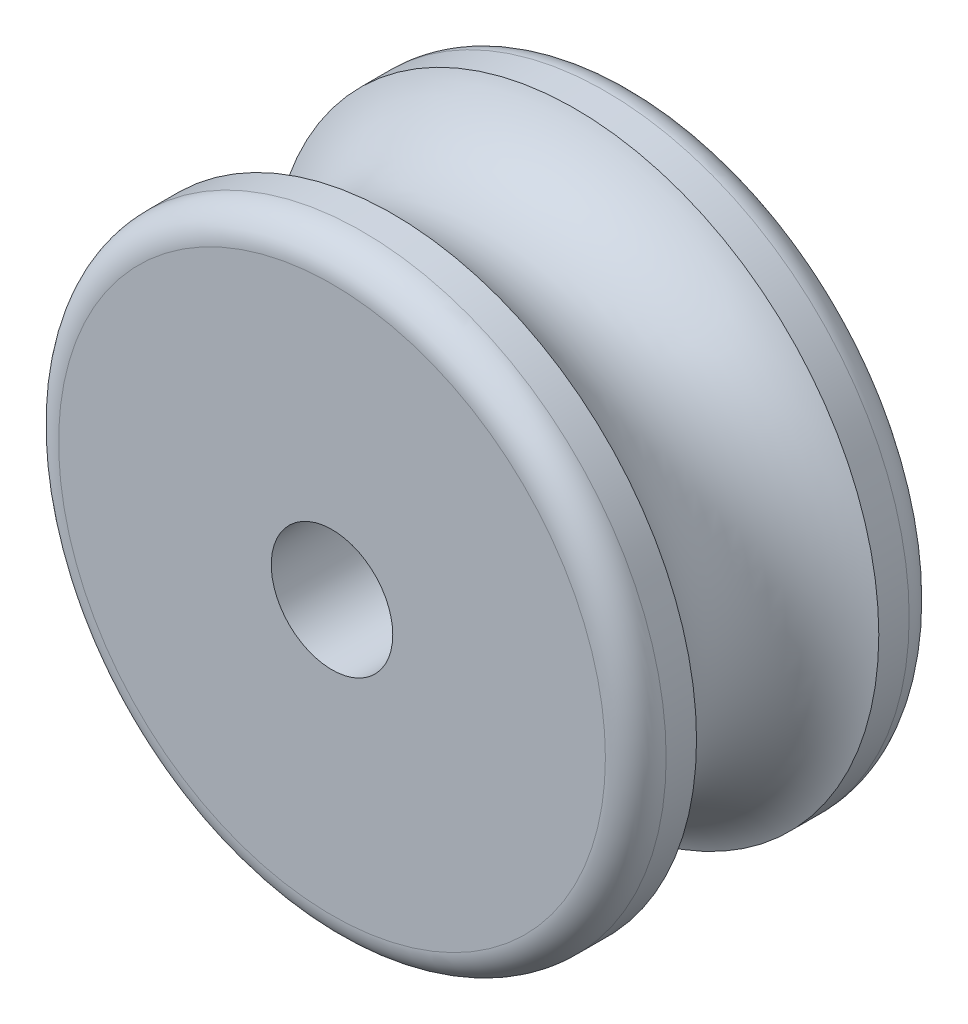
SolidWorks part; units mm, degrees
ref_plane "Front Plane" through (0, 0, 0) normal (0, 0, 1) x (1, 0, 0)
ref_plane "Top Plane" through (0, 0, 0) normal (0, 1, 0) x (1, 0, 0)
ref_plane "Right Plane" through (0, 0, 0) normal (1, 0, 0) x (0, 0, -1)
sketch "Sketch1" plane through (0, 0, 0) normal (0, 0, 1) x (1, 0, 0)
  circle A0 centre (0, 0) radius 5
  dimension "D1" = 10
extrude "Boss-Extrude1" add sketch "Sketch1" along normal blind 5
sketch "Sketch2" plane through (0, 0, 0) normal (1, 0, 0) x (0, 0, -1)
  line L0 (0, 5) -> (-5, 5) construction
  line L1 (-5, 5) -> (-5, -5) construction
  line L2 (0, 55) -> (0, -55) construction
  line L4 (-5, 0) -> (0, 0) construction
  line L5 (-4, 5) -> (-1, 5)
  arc A0 (-4, 5) -> (-1, 5) centre (-2.5, 5.625) ccw
  point P11 (-2.5, 4)
  dimension "D3" = 4
  dimension "D1" = 1
  dimension "D2" = 1
ref_axis "Axis1" through (0, 0, 5.25) along (0, 0, -1)
revolve "Cut-Revolve1" cut sketch "Sketch2" angle 360 about axis through (0, 0, 5.25) along (0, 0, -1)
fillet "Fillet1" radius 0.5 2 edges at (5, 0, 0) (5, 0, 5)
sketch "Sketch4" plane through (0, 0, 5) normal (0, 0, 1) x (1, 0, 0)
  circle A0 centre (0, 0) radius 1
  dimension "D1" = 2
extrude "Cut-Extrude1" cut sketch "Sketch4" against normal blind 5
